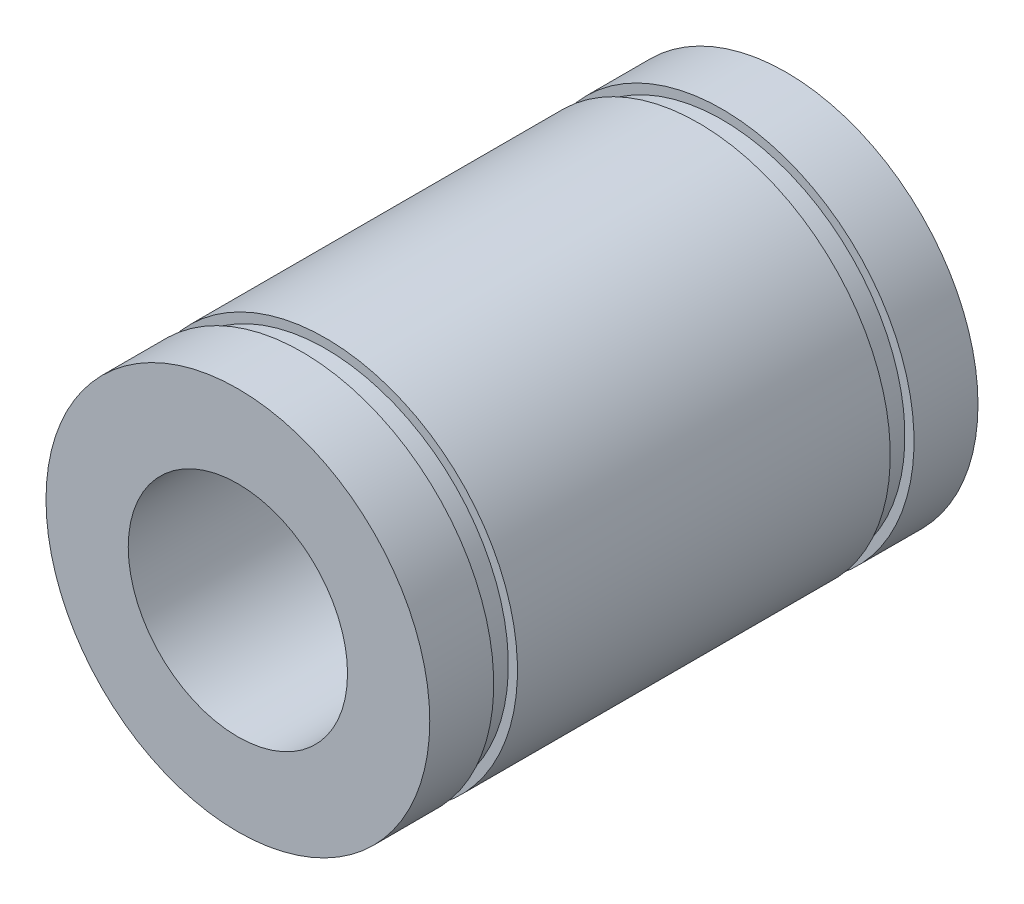
SolidWorks part; units mm, degrees
ref_plane "Plano frontal" through (0, 0, 0) normal (0, 0, 1) x (1, 0, 0)
ref_plane "Plano superior" through (0, 0, 0) normal (0, 1, 0) x (1, 0, 0)
ref_plane "Plano direito" through (0, 0, 0) normal (1, 0, 0) x (0, 0, -1)
sketch "Esboço1" plane through (0, 0, 0) normal (0, 0, 1) x (1, 0, 0)
  circle A0 centre (0, 0) radius 10.5
  dimension "D1" = 21
extrude "Ressalto-extrusão1" add sketch "Esboço1" along normal blind 30
sketch "Esboço2" plane through (0, 0, 30) normal (0, 0, 1) x (1, 0, 0)
  circle A0 centre (0, 0) radius 6
  dimension "D1" = 12
extrude "Corte-extrusão1" cut sketch "Esboço2" against normal through all both and the other way through all
sketch3d "3DSketch1"
  point P0 (-7.9386, 1.4334, 30)
sketch "Esboço4" plane through (0, 0, 0) normal (1, 0, 0) x (0, 0, -1)
  line L0 (-26.5, 10.5) -> (-26.5, 10)
  line L1 (0, 10.5) -> (-30, 10.5) construction
  line L2 (-26.5, 10) -> (-25.2, 10)
  line L3 (-25.2, 10) -> (-25.2, 10.5)
  line L4 (-25.2, 10.5) -> (-26.5, 10.5)
  line L5 (1.457, 0) -> (-32.0589, 0) construction
  line L6 (-30, 10.5) -> (-30, -10.5) construction
  line L7 (-15, 11.3853) -> (-15, -5.5647) construction
  line L8 (-4.8, 10.5) -> (-3.5, 10.5)
  line L9 (-4.8, 10) -> (-4.8, 10.5)
  line L10 (-3.5, 10) -> (-4.8, 10)
  line L11 (-3.5, 10.5) -> (-3.5, 10)
  dimension "D1" = 1.3
  dimension "D2" = 0.5
  dimension "D3" = 3.5
revolve "Corte-Revolução1" cut sketch "Esboço4" angle 360 about L5
